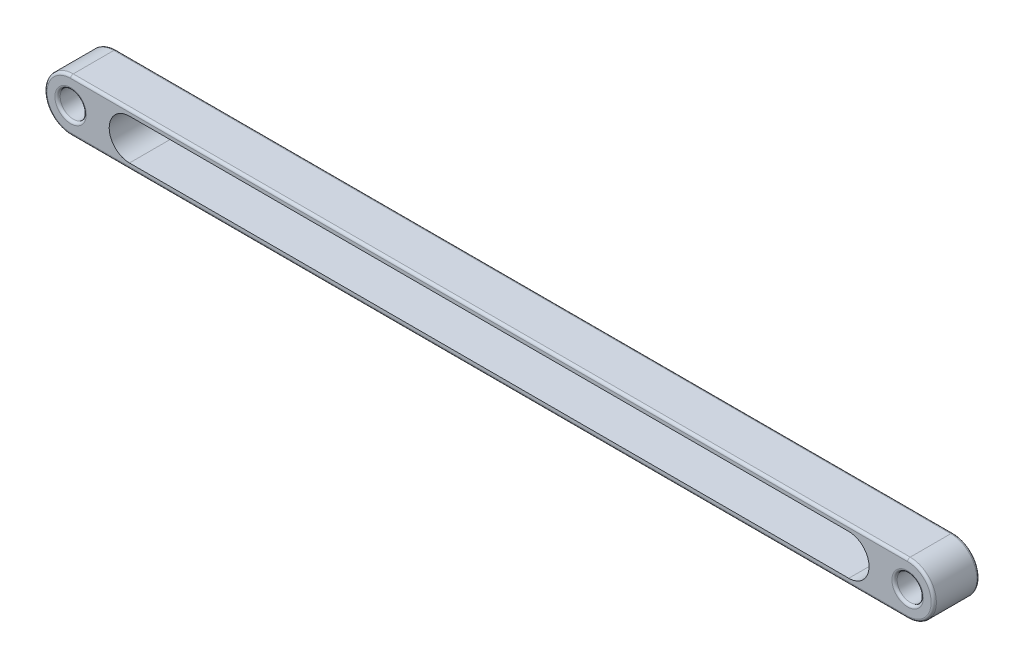
SolidWorks part; units mm, degrees
ref_plane "Front Plane" through (0, 0, 0) normal (0, 0, 1) x (1, 0, 0)
ref_plane "Top Plane" through (0, 0, 0) normal (0, 1, 0) x (1, 0, 0)
ref_plane "Right Plane" through (0, 0, 0) normal (1, 0, 0) x (0, 0, -1)
sketch "Sketch4" plane through (0, 0, 0) normal (0, 0, 1) x (1, 0, 0)
  line L0 (-320, 0) -> (320, 0) construction
  line L1 (-320, 20) -> (320, 20)
  line L2 (-320, -20) -> (320, -20)
  arc A0 (-320, 20) -> (-320, -20) centre (-320, 0) ccw
  arc A1 (320, -20) -> (320, 20) centre (320, 0) ccw
  point P3 (0, 0)
  dimension "D1" = 640
  dimension "D2" = 40
extrude "Boss-Extrude2" add sketch "Sketch4" along normal mid plane 35
sketch "Sketch5" plane through (0, 0, 17.5) normal (0, 0, 1) x (1, 0, 0)
  circle A0 centre (320, 0) radius 10
  circle A1 centre (-320, 0) radius 10
  dimension "D1" = 20
extrude "Cut-Extrude1" cut sketch "Sketch5" against normal through all
sketch "Sketch6" plane through (0, 0, -17.5) normal (0, 0, -1) x (-1, 0, 0)
  line L0 (-275, 0) -> (275, 0) construction
  line L1 (320, 0) -> (-320, 0) construction
  line L2 (-275, 15.5) -> (275, 15.5)
  line L3 (-275, -15.5) -> (275, -15.5)
  arc A0 (-275, 15.5) -> (-275, -15.5) centre (-275, 0) ccw
  arc A1 (275, -15.5) -> (275, 15.5) centre (275, 0) ccw
  point P4 (0, 0)
  dimension "D1" = 15.5
  dimension "D2" = 45
extrude "Cut-Extrude2" cut sketch "Sketch6" against normal blind 40
fillet "Fillet1" radius 2 12 edges at (340, 0, 17.5) (0, -20, 17.5) (-340, 0, 17.5) (340, 0, -17.5) (0, -20, -17.5) (-340, 0, -17.5) (0, 20, 17.5) (0, 20, -17.5) (330, 0, 17.5) (330, 0, -17.5) (-310, 0, 17.5) (-310, 0, -17.5)
